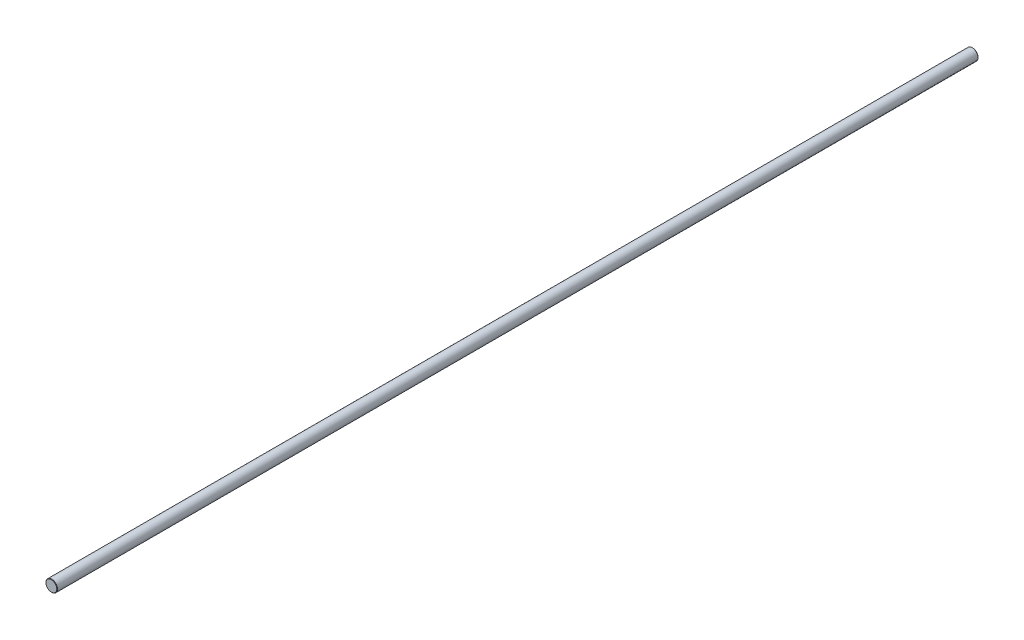
SolidWorks part; units mm, degrees
material "1.0503 (C45)"
ref_plane "Piano frontale" through (0, 0, 0) normal (0, 0, 1) x (1, 0, 0)
ref_plane "Piano superiore" through (0, 0, 0) normal (0, 1, 0) x (1, 0, 0)
ref_plane "Piano destro" through (0, 0, 0) normal (1, 0, 0) x (0, 0, -1)
sketch "Schizzo1" plane through (0, 0, 0) normal (0, 0, 1) x (1, 0, 0)
  circle A0 centre (0, 0) radius 4
  dimension "D1" = 8
extrude "Estrusione-Estrusione1" add sketch "Schizzo1" along normal blind 640
chamfer "Smusso1" distance 0.25 angle 45 2 edges at (4, 0, 0) (4, 0, 640)
